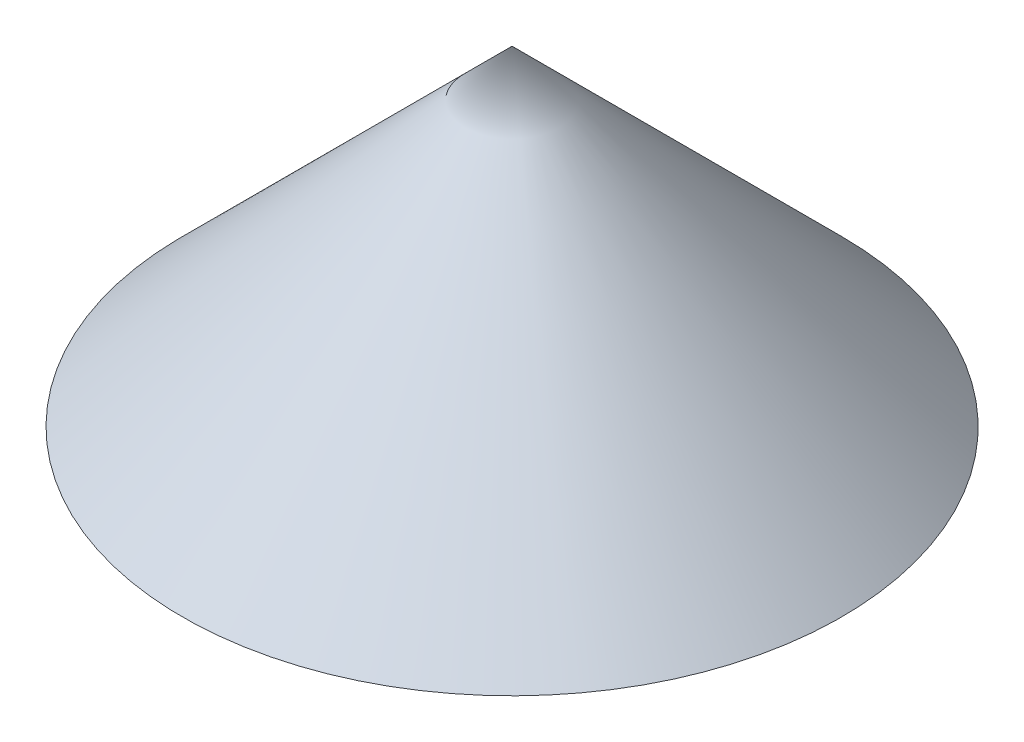
SolidWorks part; units mm, degrees
ref_plane "Front Plane" through (0, 0, 0) normal (0, 0, 1) x (1, 0, 0)
ref_plane "Top Plane" through (0, 0, 0) normal (0, 1, 0) x (1, 0, 0)
ref_plane "Right Plane" through (0, 0, 0) normal (1, 0, 0) x (0, 0, -1)
sketch "Sketch1" plane through (0, 0, 0) normal (0, 0, 1) x (1, 0, 0)
  line L0 (0, 0) -> (0, 42)
  line L1 (0, 42) -> (42, 0)
  line L2 (42, 0) -> (0, 0)
revolve "Revolve1" add sketch "Sketch1" angle 360 about L0
sketch "Sketch2" plane through (0, 0, 0) normal (0, 0, 1) x (1, 0, 0)
  line L0 (0, 0) -> (0, 38)
  line L1 (0, 38) -> (38, 0)
  line L2 (-42, 0) -> (42, 0) construction
  line L3 (38, 0) -> (0, 0)
  line L4 (0, 0) -> (6.3425, 0)
  line L5 (6.3425, 0) -> (6.3425, 31.6575)
revolve "Cut-Revolve1" cut sketch "Sketch2" angle 360 about L0
